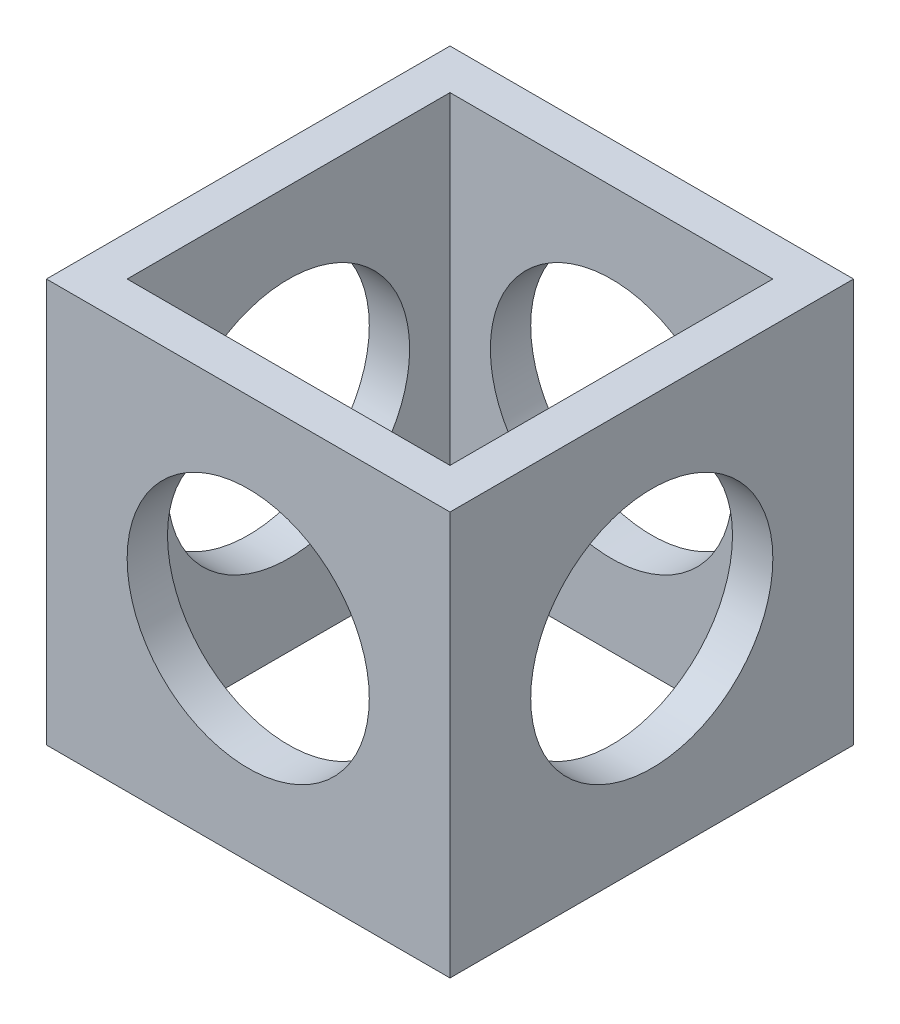
SolidWorks part; units mm, degrees
ref_plane "Front Plane" through (0, 0, 0) normal (0, 0, 1) x (1, 0, 0)
ref_plane "Top Plane" through (0, 0, 0) normal (0, 1, 0) x (1, 0, 0)
ref_plane "Right Plane" through (0, 0, 0) normal (1, 0, 0) x (0, 0, -1)
sketch "Sketch1" plane through (0, 0, 0) normal (1, 0, 0) x (0, 0, -1)
  line L5 (-25, 25) -> (25, 25)
  line L6 (-25, 25) -> (-25, -25)
  line L7 (-25, -25) -> (25, -25)
  line L8 (25, 25) -> (25, -25)
  line L9 (-25, 25) -> (25, -25) construction
  line L10 (-25, -25) -> (25, 25) construction
  point P0 (0, 0)
  dimension "D1" = 50
  dimension "D2" = 50
extrude "Boss-Extrude1" add sketch "Sketch1" against normal blind 50
sketch "Sketch2" plane through (0, 25, 0) normal (0, 1, 0) x (1, 0, 0)
  line L0 (-50, 25) -> (-50, -25) construction
  line L1 (-45, 20) -> (-5, 20)
  line L2 (-45, 20) -> (-45, -20)
  line L3 (-45, -20) -> (-5, -20)
  line L4 (-5, 20) -> (-5, -20)
  line L5 (-45, 20) -> (-5, -20) construction
  line L6 (-45, -20) -> (-5, 20) construction
  line L7 (-50, 25) -> (0, 25) construction
  point P0 (-25, 0)
  dimension "D1" = 40
  dimension "D2" = 40
  dimension "D3" = 5
  dimension "D4" = 5
extrude "Cut-Extrude1" cut sketch "Sketch2" against normal through all
sketch "Sketch4" plane through (0, 0, 0) normal (1, 0, 0) x (0, 0, -1)
  circle A0 centre (0, 0) radius 15
  dimension "D1" = 30
ref_plane "Plane2" through (-12.5, 0, -12.5) normal (0.7071, 0, 0.7071) x (0.7071, 0, -0.7071)
extrude "Cut-Extrude2" cut sketch "Sketch4" against normal through all
mirror "Mirror4" about plane through (-12.5, 0, -12.5) normal (0.7071, 0, 0.7071) of "Cut-Extrude2"
